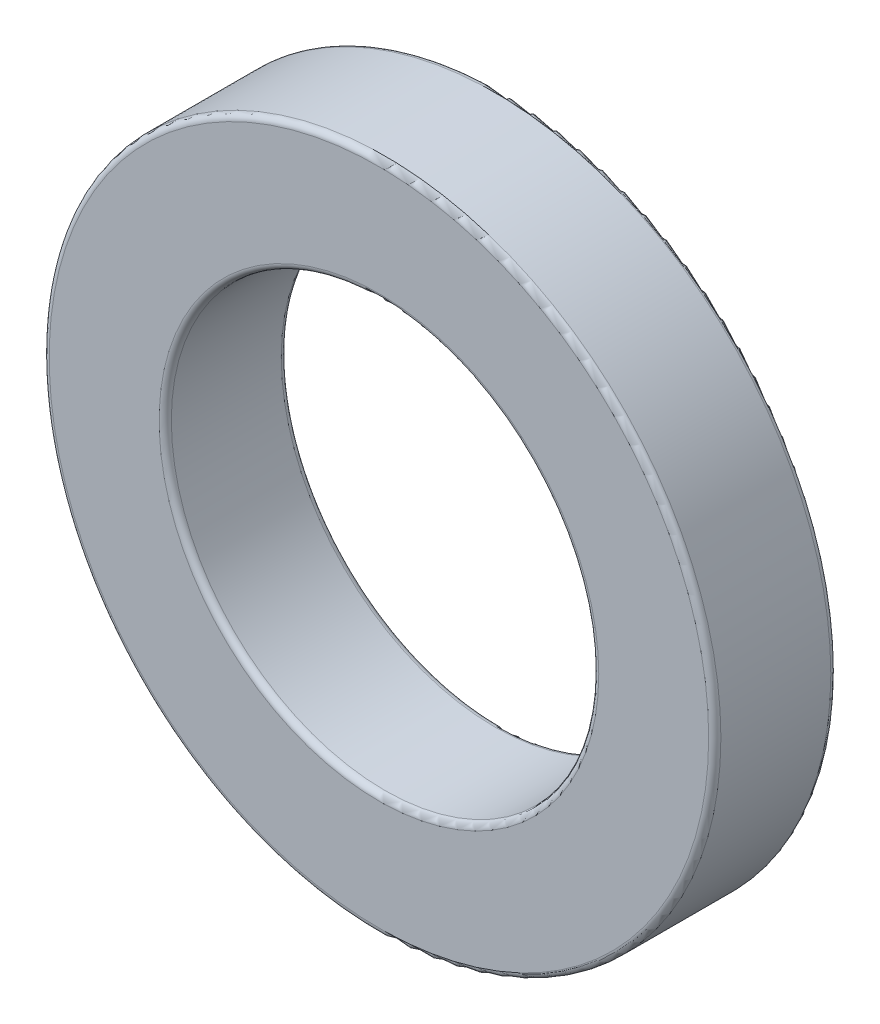
SolidWorks part; units mm, degrees
ref_plane "Plan de face" through (0, 0, 0) normal (0, 0, 1) x (1, 0, 0)
ref_plane "Plan de dessus" through (0, 0, 0) normal (0, 1, 0) x (1, 0, 0)
ref_plane "Plan de droite" through (0, 0, 0) normal (1, 0, 0) x (0, 0, -1)
sketch "Esquisse1" plane through (0, 0, 0) normal (0, 0, 1) x (1, 0, 0)
  circle A0 centre (0, 0) radius 55
  circle A1 centre (0, 0) radius 35
  dimension "D1" = 110
  dimension "D2" = 70
extrude "Boss.-Extru.1" add sketch "Esquisse1" along normal blind 20
fillet "Congé6" radius 1 4 edges at (55, 0, 0) (35, 0, 20) (55, 0, 20) (35, 0, 0)
sketch "Esquisse3" plane through (0, 0, 0) normal (0, 0, -1) x (-1, 0, 0)
  circle A0 centre (0, 0) radius 41.45
  circle A1 centre (0, 0) radius 49.95
  point P3 (-122.1318, -28.3077)
  dimension "D1" = 82.9
  dimension "D2" = 99.9
extrude "Enlèv. mat.-Extru.1" cut sketch "Esquisse3" against normal blind 4
